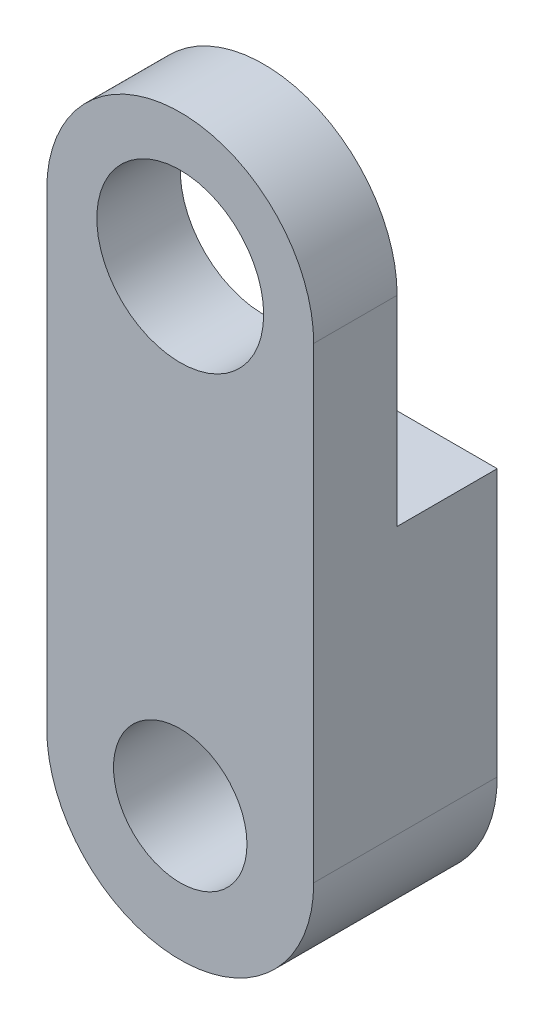
SolidWorks part; units mm, degrees
ref_plane "Plan de face" through (0, 0, 0) normal (0, 0, 1) x (1, 0, 0)
ref_plane "Plan de dessus" through (0, 0, 0) normal (0, 1, 0) x (1, 0, 0)
ref_plane "Plan de droite" through (0, 0, 0) normal (1, 0, 0) x (0, 0, -1)
sketch "Esquisse1" plane through (0, 0, 0) normal (0, 0, 1) x (1, 0, 0)
  line L0 (0, -7) -> (0, 7) construction
  line L1 (-4, -7) -> (-4, 7)
  line L2 (4, -7) -> (4, 7)
  arc A0 (-4, -7) -> (4, -7) centre (0, -7) ccw
  arc A1 (4, 7) -> (-4, 7) centre (0, 7) ccw
  circle A2 centre (0, -7) radius 2
  circle A3 centre (0, 7) radius 2.5
  point P2 (0, 0)
  dimension "D1" = 4
  dimension "D2" = 4
  dimension "D3" = 5
  dimension "D4" = 14
extrude "Boss.-Extru.1" add sketch "Esquisse1" along normal blind 5.5
sketch "Esquisse2" plane through (0, 0, 0) normal (1, 0, 0) x (0, 0, -1)
  line L1 (-3, 1) -> (0, 1)
  line L2 (-3, 1) -> (-3, 11)
  line L3 (-3, 11) -> (0, 11)
  line L4 (0, 1) -> (0, 11)
  line L6 (-5.5, 7) -> (0, 7) construction
  dimension "D1" = 6
  dimension "D2" = 3
extrude "Enlèv. mat.-Extru.1" cut sketch "Esquisse2" against normal through all both and the other way through all
